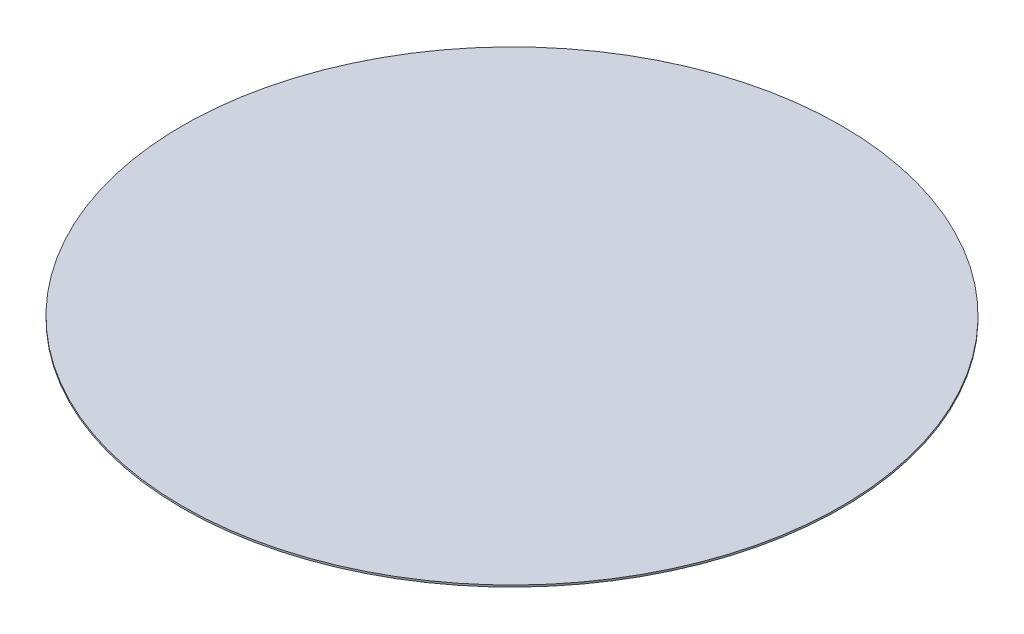
SolidWorks part; units mm, degrees
material "Pino"
ref_plane "Front Plane" through (0, 0, 0) normal (0, 0, 1) x (1, 0, 0)
ref_plane "Top Plane" through (0, 0, 0) normal (0, 1, 0) x (1, 0, 0)
ref_plane "Right Plane" through (0, 0, 0) normal (1, 0, 0) x (0, 0, -1)
sketch "Croquis1" plane through (0, 0, 0) normal (0, 1, 0) x (1, 0, 0)
  circle A0 centre (0, 0) radius 550
  dimension "D1" = 1100
extrude "Saliente-Extruir1" add sketch "Croquis1" along normal blind 3
